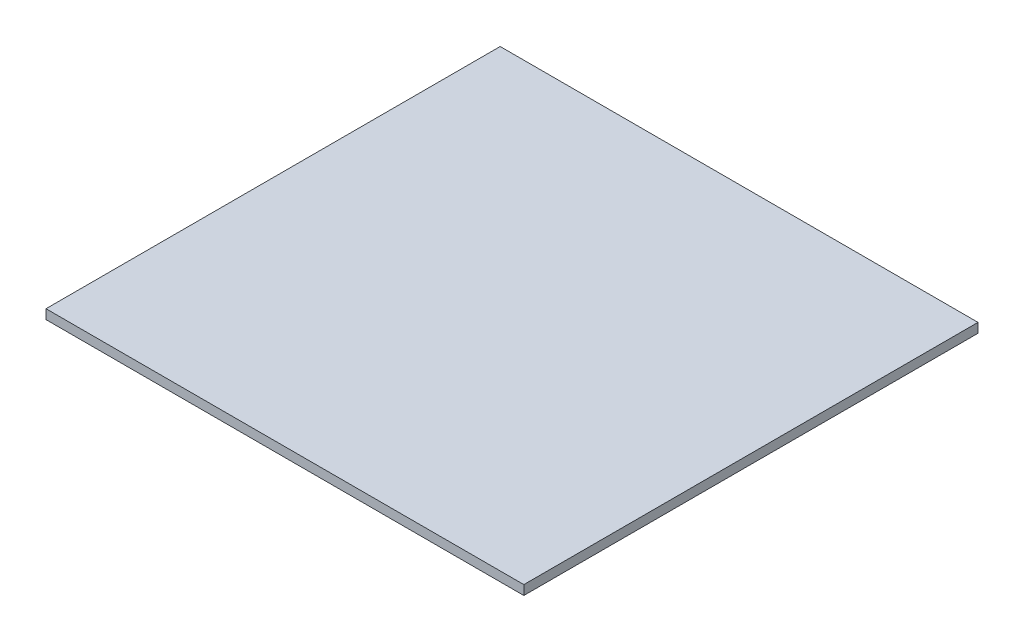
SolidWorks part; units mm, degrees
ref_plane "Alzado" through (0, 0, 0) normal (0, 0, 1) x (1, 0, 0)
ref_plane "Planta" through (0, 0, 0) normal (0, 1, 0) x (1, 0, 0)
ref_plane "Vista lateral" through (0, 0, 0) normal (1, 0, 0) x (0, 0, -1)
sketch "Croquis1" plane through (0, 0, 0) normal (0, 1, 0) x (1, 0, 0)
  line L1 (265.3147, -307.6687) -> (-239.6853, -307.6687)
  line L2 (265.3147, -307.6687) -> (265.3147, 172.3313)
  line L3 (265.3147, 172.3313) -> (-239.6853, 172.3313)
  line L4 (-239.6853, -307.6687) -> (-239.6853, 172.3313)
  line L5 (265.3147, -307.6687) -> (-239.6853, 172.3313) construction
  line L6 (265.3147, 172.3313) -> (-239.6853, -307.6687) construction
  dimension "D1" = 505
  dimension "D2" = 480
extrude "Saliente-Extruir1" add sketch "Croquis1" along normal blind 10
